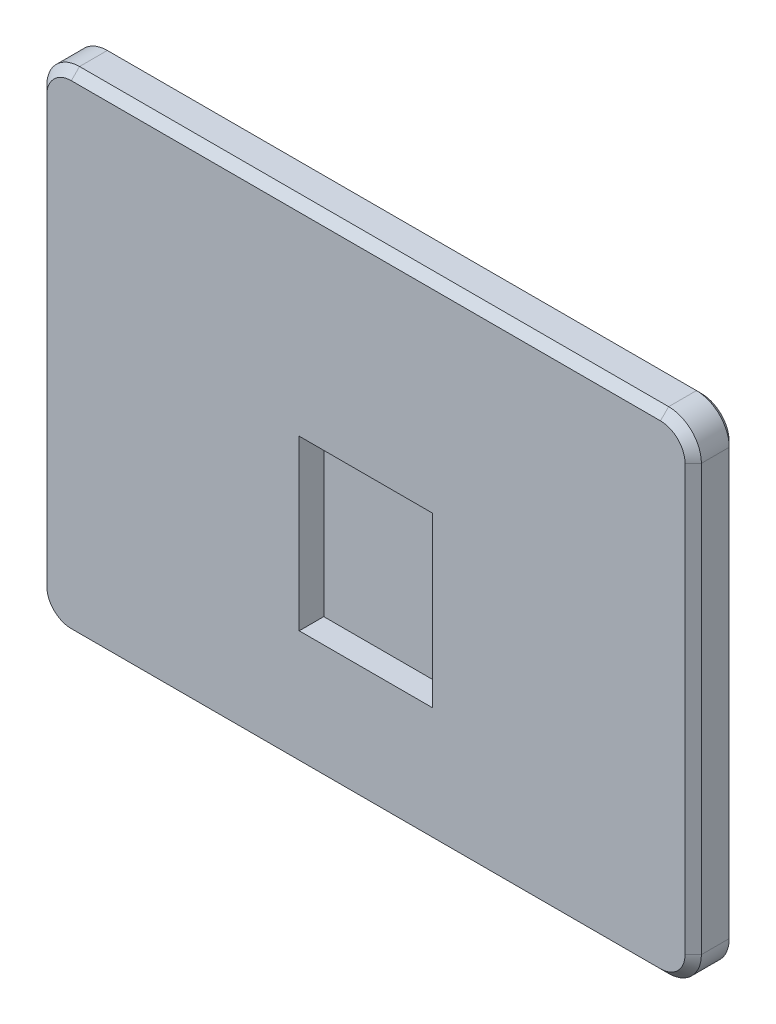
SolidWorks part; units mm, degrees
ref_plane "Front Plane" through (0, 0, 0) normal (0, 0, 1) x (1, 0, 0)
ref_plane "Top Plane" through (0, 0, 0) normal (0, 1, 0) x (1, 0, 0)
ref_plane "Right Plane" through (0, 0, 0) normal (1, 0, 0) x (0, 0, -1)
sketch "Sketch1" plane through (0, 0, 0) normal (0, 0, 1) x (1, 0, 0)
  line L1 (-20, -15) -> (20, -15)
  line L2 (-20, -15) -> (-20, 15)
  line L3 (-20, 15) -> (20, 15)
  line L4 (20, -15) -> (20, 15)
  line L5 (-20, -15) -> (20, 15) construction
  line L6 (-20, 15) -> (20, -15) construction
  point P0 (0, 0)
  dimension "D1" = 30
  dimension "D2" = 40
extrude "Boss-Extrude1" add sketch "Sketch1" along normal blind 2.5
sketch "Sketch2" plane through (0, 0, 2.5) normal (0, 0, 1) x (1, 0, 0)
  line L1 (-4.075, -7.65) -> (4.075, -7.65)
  line L2 (-4.075, -7.65) -> (-4.075, 2.65)
  line L3 (-4.075, 2.65) -> (4.075, 2.65)
  line L4 (4.075, -7.65) -> (4.075, 2.65)
  line L5 (-4.075, -7.65) -> (4.075, 2.65) construction
  line L6 (-4.075, 2.65) -> (4.075, -7.65) construction
  point P0 (0, -2.5)
  dimension "D1" = 8.15
  dimension "D2" = 10.3
  dimension "D3" = 2.5
extrude "Cut-Extrude1" cut sketch "Sketch2" against normal blind 1.5
fillet "Fillet1" radius 2 4 edges at (-20, -15, 1.25) (20, -15, 1.25) (-20, 15, 1.25) (20, 15, 1.25)
chamfer "Chamfer1" distance 0.5 angle 45 8 edges at (0, -15, 2.5) (19.4142, -14.4142, 2.5) (-19.4142, -14.4142, 2.5) (20, 0, 2.5) (-20, 0, 2.5) (19.4142, 14.4142, 2.5) (-19.4142, 14.4142, 2.5) (0, 15, 2.5)
chamfer "Chamfer2" distance 0.3 angle 45 8 edges at (19.4142, -14.4142, 0) (20, 0, 0) (19.4142, 14.4142, 0) (0, 15, 0) (-19.4142, 14.4142, 0) (-20, 0, 0) (-19.4142, -14.4142, 0) (0, -15, 0)
